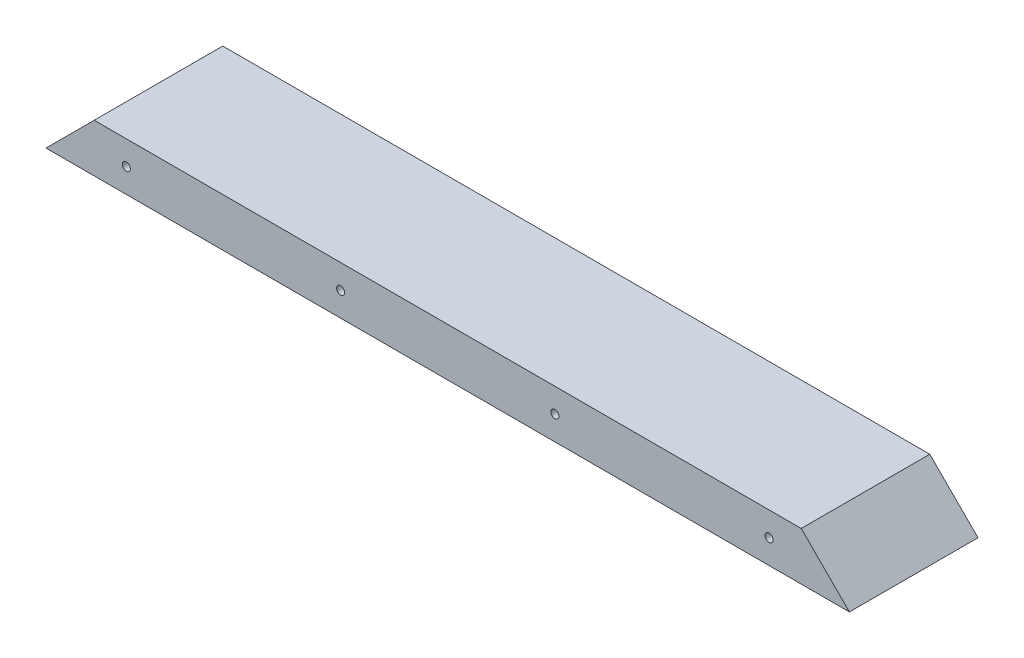
SolidWorks part; units mm, degrees
ref_plane "Alzado" through (0, 0, 0) normal (0, 0, 1) x (1, 0, 0)
ref_plane "Planta" through (0, 0, 0) normal (0, 1, 0) x (1, 0, 0)
ref_plane "Vista lateral" through (0, 0, 0) normal (1, 0, 0) x (0, 0, -1)
sketch "Croquis1" plane through (0, 0, 0) normal (1, 0, 0) x (0, 0, -1)
  line L0 (-20, 0) -> (20, 0)
  line L1 (20, 0) -> (20, 15)
  line L2 (20, 15) -> (18.5, 15)
  line L6 (-18.5, 15) -> (-20, 15)
  line L7 (-20, 15) -> (-20, 0)
  line L8 (-18.5, 15) -> (18.5, 15)
  point P4 (0, 0)
extrude "Saliente-Extruir1" add sketch "Croquis1" along normal blind 250
sketch "Croquis2" plane through (0, 0, -20) normal (0, 0, -1) x (-1, 0, 0)
  line L3 (0, 15) -> (-15, 15)
  line L4 (-250, 15) -> (0, 15) construction
  line L5 (-15, 15) -> (0, 0)
  line L6 (0, 0) -> (0, 15)
  line L7 (-250, 15) -> (-235, 15)
  line L8 (-235, 15) -> (-250, 0)
  line L9 (-250, 0) -> (0, 0) construction
  line L10 (-250, 0) -> (-250, 15) construction
  line L11 (-250, 0) -> (-250, 15)
  line L12 (-125, 0) -> (-125, 15) construction
  line L13 (-125, 0) -> (-125, 7.5) construction
  line L14 (-25, 7.5) -> (-91.6667, 7.5) construction
  line L15 (-91.6667, 7.5) -> (-158.3333, 7.5) construction
  line L16 (-242.5, 7.5) -> (-225, 7.5) construction
  line L17 (-158.3333, 7.5) -> (-225, 7.5) construction
  line L18 (-225, 7.5) -> (-242.5, 7.5) construction
  line L21 (-250, 15) -> (0, 15) construction
  circle A7 centre (-225, 7.5) radius 1.25
  circle A8 centre (-25, 7.5) radius 1.25
  circle A9 centre (-158.3333, 7.5) radius 1.25
  circle A10 centre (-91.6667, 7.5) radius 1.25
  point P29 (-125, 0)
extrude "Cortar-Extruir1" cut sketch "Croquis2" against normal through all
